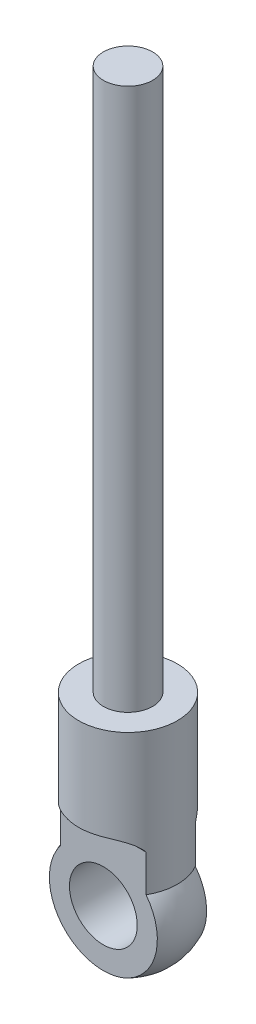
SolidWorks part; units mm, degrees
material "1060 Alloy"
ref_plane "Front Plane" through (0, 0, 0) normal (0, 0, 1) x (1, 0, 0)
ref_plane "Top Plane" through (0, 0, 0) normal (0, 1, 0) x (1, 0, 0)
ref_plane "Right Plane" through (0, 0, 0) normal (1, 0, 0) x (0, 0, -1)
sketch "Sketch1" plane through (0, 0, 0) normal (0, 0, 1) x (1, 0, 0)
  line L0 (0, 0) -> (0, 44)
  line L1 (0, 0) -> (0, -19)
  line L2 (0, 44) -> (-2, 44)
  line L3 (-2, 44) -> (-2, 0)
  line L4 (-2, 0) -> (-4, 0)
  line L5 (-4, 0) -> (-4, -11.5)
  line L6 (-12.3945, -19) -> (12.915, -19) construction
  arc A1 (0, -19) -> (-4, -11.5) centre (0, -14.1833) cw
  dimension "D1" = 44
  dimension "D2" = 19
  dimension "D3" = 2
  dimension "D4" = 2
  dimension "D5" = 11.5
revolve "Revolve1" add sketch "Sketch1" angle 360 about L0
sketch "Sketch2" plane through (0, 0, 0) normal (1, 0, 0) x (0, 0, -1)
  line L0 (-4, 0) -> (-4, -7.5)
  line L1 (-4, 0) -> (-4, -11.5) construction
  line L2 (-2, -7.5) -> (-2, -18.5651)
  line L3 (0, 0) -> (0, -19) construction
  line L4 (2, -7.5) -> (2, -18.5651)
  line L5 (4, -11.5) -> (-4, -11.5) construction
  line L6 (4, -7.5) -> (4, 0)
  line L7 (4, 0) -> (-4, 0)
  line L8 (4, -8.078) -> (4, -7.5)
  line L11 (-4, -8.078) -> (-4, -7.5)
  arc A0 (-4, -11.5) -> (4, -11.5) centre (0, -14.1833) ccw construction
  arc A1 (-4, -7.5) -> (-2, -11.5) centre (-4, -10) cw
  arc A2 (4, -7.5) -> (2, -11.5) centre (4, -10) ccw
  arc A3 (4, -8.078) -> (2, -18.5651) centre (0, -12.7494) cw
  arc A4 (-4, -8.078) -> (-2, -18.5651) centre (0, -12.7494) ccw
  dimension "D3" = 6.15
  dimension "D1" = 7.5
  dimension "D2" = 4
extrude "Cut-Extrude1" cut sketch "Sketch2" against normal blind 10 and the other way through all contours L11 A4 L2 A1 | A3 L8 A2 L4
sketch "Sketch3" plane through (0, 0, 2) normal (0, 0, 1) x (1, 0, 0)
  line L0 (0, 0) -> (0, -18.5651) construction
  arc A0 (-3.4641, -11.5) -> (3.4641, -11.5) centre (0, -14.1833) ccw construction
  circle A1 centre (0, -14) radius 2.75
  dimension "D1" = 5.5
  dimension "D2" = 14
extrude "Cut-Extrude2" cut sketch "Sketch3" against normal through all and the other way through all
sketch "Sketch4" plane through (0, 0, 0) normal (0, 0, 1) x (1, 0, 0)
  circle A0 centre (0, -14) radius 2.75 construction
  circle A1 centre (0, -14) radius 2.75
